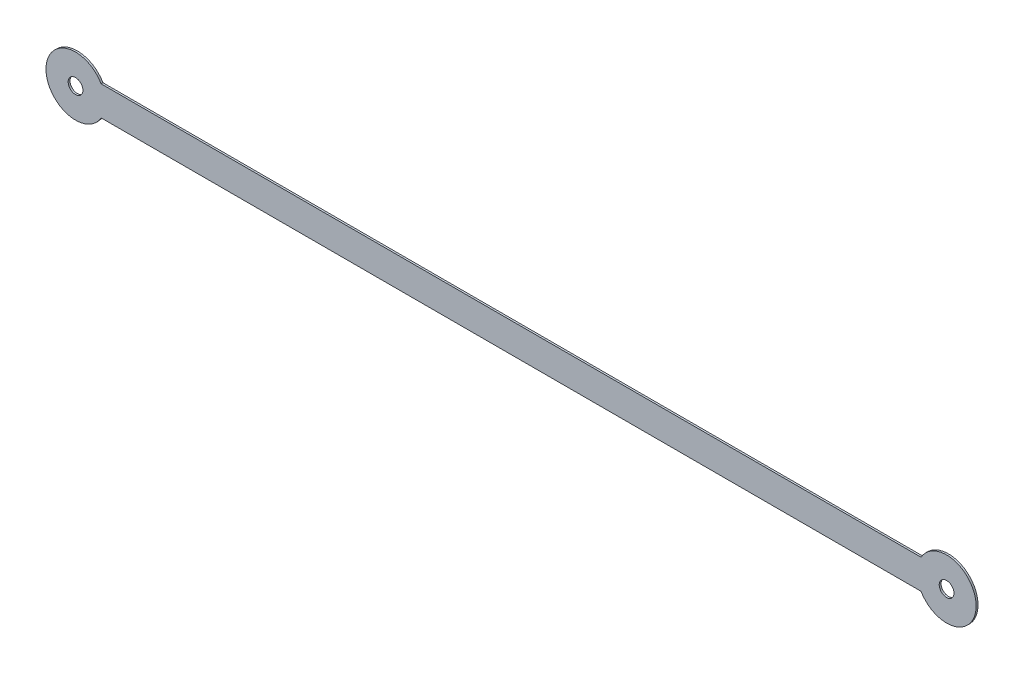
SolidWorks part; units mm, degrees
ref_plane "Front Plane" through (0, 0, 0) normal (0, 0, 1) x (1, 0, 0)
ref_plane "Top Plane" through (0, 0, 0) normal (0, 1, 0) x (1, 0, 0)
ref_plane "Right Plane" through (0, 0, 0) normal (1, 0, 0) x (0, 0, -1)
sketch "Sketch1" plane through (0, 0, 0) normal (0, 0, 1) x (1, 0, 0)
  line L0 (0, 0) -> (118, 0) construction
  line L1 (0, 4) -> (118, 4)
  line L2 (0, -4) -> (118, -4)
  circle A0 centre (0, 0) radius 1
  circle A1 centre (118, 0) radius 1
  arc A2 (0, 4) -> (0, -4) centre (0, 0) ccw
  arc A3 (118, -4) -> (118, 4) centre (118, 0) ccw
  point P5 (59, 0)
  dimension "D1" = 2
  dimension "D3" = 4
  dimension "D2" = 118
extrude "Boss-Extrude1" add sketch "Sketch1" along normal blind 0.254
sketch "Sketch2" plane through (0, 0, 0) normal (0, 0, -1) x (-1, 0, 0)
  line L0 (-118, 0) -> (0, 0) construction
  line L1 (-114.5359, 2) -> (-3.4641, 2)
  line L2 (-114.5359, -2) -> (-3.4641, -2)
  line L3 (0, 4) -> (-118, 4)
  line L4 (0, -4) -> (-118, -4)
  arc A0 (-118, -4) -> (-114.5359, -2) centre (-118, 0) ccw
  arc A1 (0, 4) -> (-3.4641, 2) centre (0, 0) ccw
  arc A2 (-3.4641, -2) -> (0, -4) centre (0, 0) ccw
  arc A3 (-114.5359, 2) -> (-118, 4) centre (-118, 0) ccw
  dimension "D1" = 4
extrude "Cut-Extrude1" cut sketch "Sketch2" against normal through all
equation "\"orig_diameter\"= 50.8mm"
equation "\"scale_factor\"= 1.08"
equation "\"d\"= \"orig_diameter\" * \"scale_factor\""
